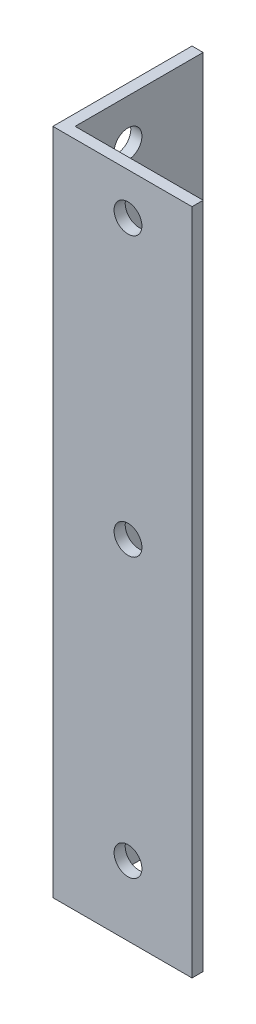
SolidWorks part; units mm, degrees
ref_plane "Спереди" through (0, 0, 0) normal (0, 0, 1) x (1, 0, 0)
ref_plane "Сверху" through (0, 0, 0) normal (0, 1, 0) x (1, 0, 0)
ref_plane "Справа" through (0, 0, 0) normal (1, 0, 0) x (0, 0, -1)
sketch "Эскиз1" plane through (0, 0, 0) normal (0, 1, 0) x (1, 0, 0)
  line L0 (0, 0) -> (50, 0)
  line L1 (0, 0) -> (0, 50)
extrude "Вытянуть-Тонкостенный1" add sketch "Эскиз1" along normal blind 240 thin thin type one direction wall 4
sketch "Эскиз2" plane through (0, 0, 0) normal (0, 0, 1) x (1, 0, 0)
  circle A0 centre (27, 225) radius 5
  circle A1 centre (27, 125) radius 5
  circle A2 centre (27, 25) radius 5
  dimension "D1" = 3
extrude "Вырез-Вытянуть1" cut sketch "Эскиз2" against normal blind 10
sketch "Эскиз3" plane through (0, 0, 0) normal (-1, 0, 0) x (0, 0, 1)
  circle A0 centre (-23, 225) radius 5
  circle A1 centre (-23, 125) radius 5
  circle A2 centre (-23, 25) radius 5
  dimension "D1" = 3
extrude "Вырез-Вытянуть2" cut sketch "Эскиз3" against normal blind 10
